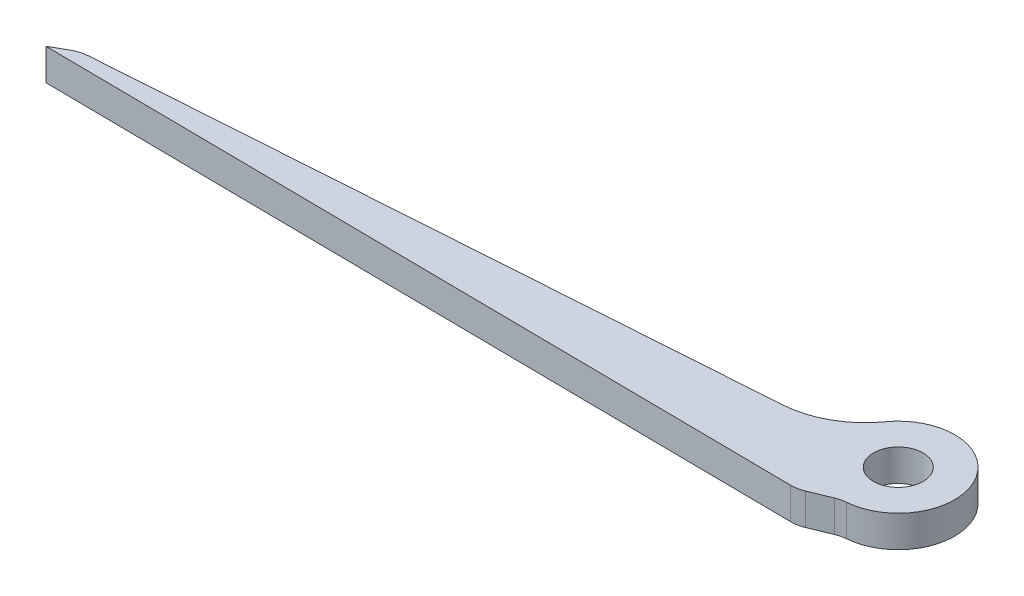
SolidWorks part; units mm, degrees
ref_plane "Front Plane" through (0, 0, 0) normal (0, 0, 1) x (1, 0, 0)
ref_plane "Top Plane" through (0, 0, 0) normal (0, 1, 0) x (1, 0, 0)
ref_plane "Right Plane" through (0, 0, 0) normal (1, 0, 0) x (0, 0, -1)
other "Bounding Box"
ref_plane "Default Plane" through (-8.9266, -12.7485, 0) normal (-0.1736, 0.9848, 0) x (0.9848, 0.1736, 0)
sketch "Sketch1" plane through (0, 0, 0) normal (0, 1, 0) x (1, 0, 0)
  line L0 (-5.6642, 0) -> (-77.1792, -4.9356)
  line L1 (-77.1792, -4.9356) -> (-79.392, -6.1825)
  line L2 (-79.392, -6.1825) -> (-3.192, -6.9784)
  line L3 (-3.192, -6.9784) -> (0, -5.6642)
  circle A0 centre (0, 0) radius 2.4892
  arc A1 (0, -5.6642) -> (-5.6642, 0) centre (0, 0) ccw
  point P5 (-5.6642, 0)
  point P9 (-38.0833, -5.6642)
  point P10 (-31.8075, -3.4201)
  point P11 (-38.0369, -6.1825)
  point P12 (-36.2301, -5.6642)
  point P13 (-36.6062, -5.2975)
  dimension "D1" = 4.9784
  dimension "D2" = 3.175
  dimension "D3" = 76.2
  dimension "D4" = 2.54
  dimension "D5" = 30
  dimension "D6" = 71.6851
  dimension "D7" = 154.546
  dimension "D8" = 7.132
extrude "Boss-Extrude1" add sketch "Sketch1" along normal blind 3.175
fillet "Fillet1" radius 3.175 3 edges at (-77.1792, 1.5875, 4.9356) (-3.192, 1.5875, 6.9784) (0, 1.5875, 5.6642)
fillet "Fillet2" radius 8.89 1 edges at (-5.6642, 1.5875, 0)
